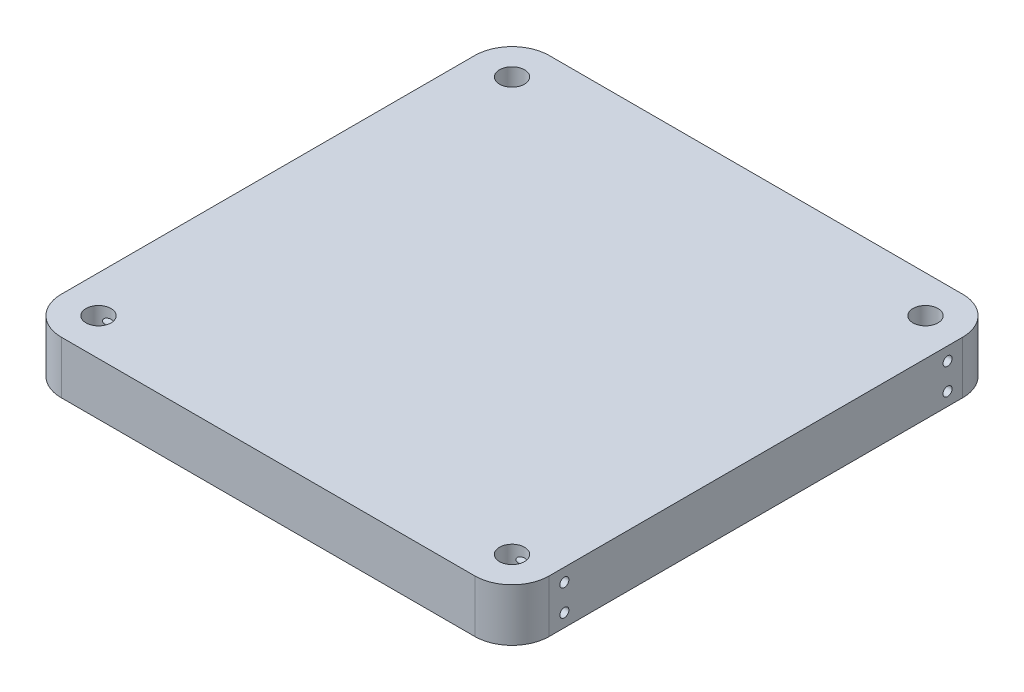
SolidWorks part; units mm, degrees
ref_plane "Front Plane" through (0, 0, 0) normal (0, 0, 1) x (1, 0, 0)
ref_plane "Top Plane" through (0, 0, 0) normal (0, 1, 0) x (1, 0, 0)
ref_plane "Right Plane" through (0, 0, 0) normal (1, 0, 0) x (0, 0, -1)
sketch "Sketch1" plane through (0, 0, 0) normal (0, 1, 0) x (1, 0, 0)
  line L1 (-50, 50) -> (50, 50) construction
  line L2 (-50, 59) -> (50, 59)
  line L3 (-59, 50) -> (-59, -50)
  line L4 (50, 50) -> (50, -50) construction
  line L5 (-50, -59) -> (50, -59)
  line L6 (50, -50) -> (-50, -50) construction
  line L7 (-50, -50) -> (-50, 50) construction
  line L8 (59, 50) -> (59, -50)
  line L9 (-59, 59) -> (59, -59) construction
  line L10 (-59, -59) -> (59, 59) construction
  circle A0 centre (50, 50) radius 3.025
  circle A1 centre (50, -50) radius 3.025
  circle A2 centre (-50, 50) radius 3.025
  circle A3 centre (-50, -50) radius 3.025
  arc A4 (-59, -50) -> (-50, -59) centre (-50, -50) ccw
  arc A5 (50, -59) -> (59, -50) centre (50, -50) ccw
  arc A6 (50, 59) -> (59, 50) centre (50, 50) cw
  arc A7 (-50, 59) -> (-59, 50) centre (-50, 50) ccw
  point P8 (50, 0)
  point P9 (0, 50)
  point P10 (0, 0)
  point P11 (-50, 0)
  point P12 (0, -50)
  dimension "D1" = 6.05
  dimension "D4" = 9
  dimension "D2" = 100
  dimension "D3" = 9
extrude "Boss-Extrude1" add sketch "Sketch1" along normal blind 12.7
sketch "Sketch2" plane through (59, 0, 0) normal (1, 0, 0) x (0, 0, -1)
  line L0 (46.34, 12.7) -> (46.975, 12.7) construction
  line L1 (46.34, 12.7) -> (46.34, 9.525) construction
  line L2 (-50, 12.7) -> (50, 12.7) construction
  line L3 (46.34, 9.525) -> (46.34, 3.175) construction
  line L4 (46.34, 3.175) -> (46.34, 0) construction
  line L5 (-50, 0) -> (50, 0) construction
  line L6 (-46.34, 12.7) -> (-46.34, 9.525) construction
  line L7 (-46.34, 9.525) -> (-46.34, 3.175) construction
  line L8 (-46.34, 3.175) -> (-46.34, 0) construction
  line L9 (-46.975, 12.7) -> (-46.34, 12.7) construction
  circle A0 centre (-46.34, 9.525) radius 1.095
  circle A1 centre (-46.34, 3.175) radius 1.095
  circle A2 centre (46.34, 9.525) radius 1.095
  circle A3 centre (46.34, 3.175) radius 1.095
  dimension "D1" = 2.19
  dimension "D2" = 3.175
  dimension "D3" = 0.635
extrude "Cut-Extrude1" cut sketch "Sketch2" against normal blind 15
mirror "Mirror1" about plane through (0, 0, 0) normal (1, 0, 0) of "Cut-Extrude1"
